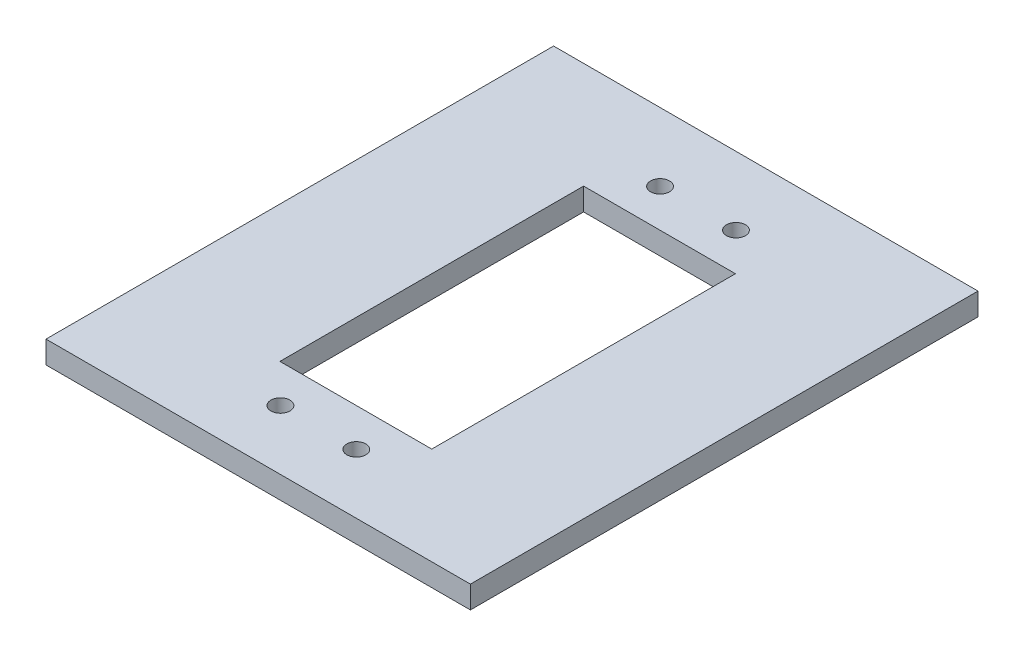
SolidWorks part; units mm, degrees
ref_plane "Front Plane" through (0, 0, 0) normal (0, 0, 1) x (1, 0, 0)
ref_plane "Top Plane" through (0, 0, 0) normal (0, 1, 0) x (1, 0, 0)
ref_plane "Right Plane" through (0, 0, 0) normal (1, 0, 0) x (0, 0, -1)
sketch "Sketch1" plane through (0, 0, 0) normal (0, 1, 0) x (1, 0, 0)
  line L1 (-24.7477, 34.1827) -> (31.1523, 34.1827)
  line L2 (-24.7477, 34.1827) -> (-24.7477, -32.6773)
  line L3 (-24.7477, -32.6773) -> (31.1523, -32.6773)
  line L4 (31.1523, 34.1827) -> (31.1523, -32.6773)
  dimension "D1" = 55.9
  dimension "D2" = 66.86
extrude "Boss-Extrude1" add sketch "Sketch1" along normal blind 2.95
sketch "Sketch3" plane through (0, 2.95, 0) normal (0, 1, 0) x (1, 0, 0)
  line L1 (-6.7977, 20.1827) -> (13.2023, 20.1827)
  line L2 (-6.7977, 20.1827) -> (-6.7977, -19.8173)
  line L3 (-6.7977, -19.8173) -> (13.2023, -19.8173)
  line L4 (13.2023, 20.1827) -> (13.2023, -19.8173)
  line L5 (31.1523, -32.6773) -> (31.1523, 34.1827) construction
  line L7 (31.1523, 34.1827) -> (-24.7477, 34.1827) construction
  dimension "D3" = 14
  dimension "D4" = 17.95
  dimension "D1" = 20
  dimension "D2" = 40
extrude "Cut-Extrude1" cut sketch "Sketch3" against normal blind 6.86
sketch "Sketch4" plane through (0, 2.95, 0) normal (0, 1, 0) x (1, 0, 0)
  circle A0 centre (-1.7296, 25.1827) radius 1.25
  circle A1 centre (8.2704, 25.1827) radius 1.25
  circle A2 centre (-1.7296, -24.8173) radius 1.25
  circle A3 centre (8.2704, -24.8173) radius 1.25
  dimension "D1" = 2
  dimension "D4" = 7.1194
  dimension "D2" = 7.023
  dimension "D5" = 7.1194
  dimension "D6" = 7.023
  dimension "D3" = 2
extrude "Cut-Extrude2" cut sketch "Sketch4" against normal blind 6.86
